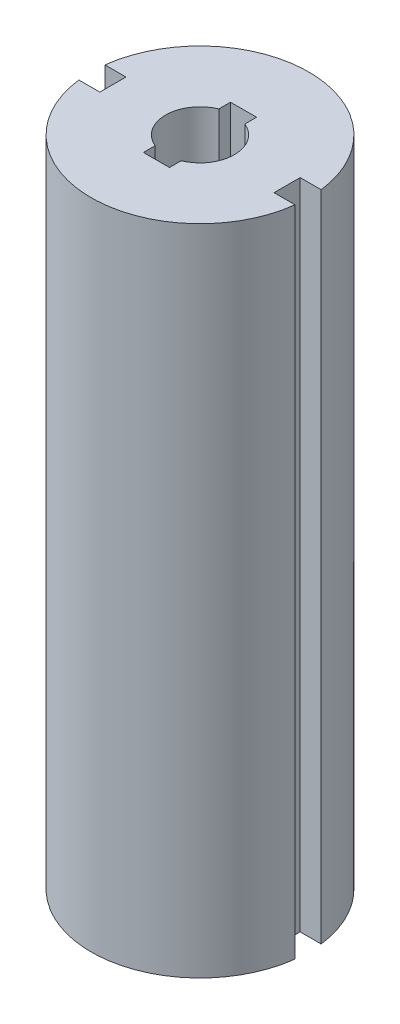
SolidWorks part; units mm, degrees
material "ABS"
ref_plane "Front Plane" through (0, 0, 0) normal (0, 0, 1) x (1, 0, 0)
ref_plane "Top Plane" through (0, 0, 0) normal (0, 1, 0) x (1, 0, 0)
ref_plane "Right Plane" through (0, 0, 0) normal (1, 0, 0) x (0, 0, -1)
sketch "Sketch1" plane through (0, 0, 0) normal (0, 1, 0) x (1, 0, 0)
  line L0 (0, 0) -> (0, 0.5711) construction
  line L1 (2.54, -0.381) -> (3.1521, -0.381)
  line L2 (-2.54, -0.381) -> (-3.1521, -0.381)
  line L3 (-2.54, -0.381) -> (-2.54, 0.381)
  line L4 (-2.54, 0.381) -> (-3.1521, 0.381)
  line L5 (2.54, -0.381) -> (2.54, 0.381)
  line L6 (-2.54, -0.381) -> (-3.175, 0) construction
  line L7 (-2.54, 0.381) -> (-3.175, 0) construction
  line L8 (2.54, 0.381) -> (3.1521, 0.381)
  arc A0 (-3.1521, -0.381) -> (3.1521, -0.381) centre (0, 0) ccw
  arc A1 (3.1521, 0.381) -> (-3.1521, 0.381) centre (0, 0) ccw
  point P3 (-3.175, 0)
  dimension "D1" = 6.35
  dimension "D2" = 0.762
  dimension "D3" = 0.635
extrude "Boss-Extrude1" add sketch "Sketch1" along normal blind 19.05
sketch "Sketch2" plane through (0, 19.05, 0) normal (0, 1, 0) x (1, 0, 0)
  line L0 (-0.3802, 0.9285) -> (-0.3802, 1.27)
  line L1 (-0.3802, -1.27) -> (0.3802, -1.27)
  line L2 (-0.3802, -1.27) -> (-0.3802, -0.9285)
  line L3 (-0.3802, 1.27) -> (0.3802, 1.27)
  line L4 (0.3802, -1.27) -> (0.3802, -0.9285)
  line L5 (-0.3802, -1.27) -> (0.3802, 1.27) construction
  line L6 (-0.3802, 1.27) -> (0.3802, -1.27) construction
  line L7 (0.3802, 0.9285) -> (0.3802, 1.27)
  arc A0 (-0.3802, 0.9285) -> (-0.3802, -0.9285) centre (0, 0) ccw
  arc A1 (0.3802, -0.9285) -> (0.3802, 0.9285) centre (0, 0) ccw
  dimension "D1" = 2.0066
  dimension "D2" = 2.54
  dimension "D3" = 0.7604
extrude "Cut-Extrude1" cut sketch "Sketch2" against normal blind 7.62 contours A0 L2 L1 L4 A1 L7 L3 L0
